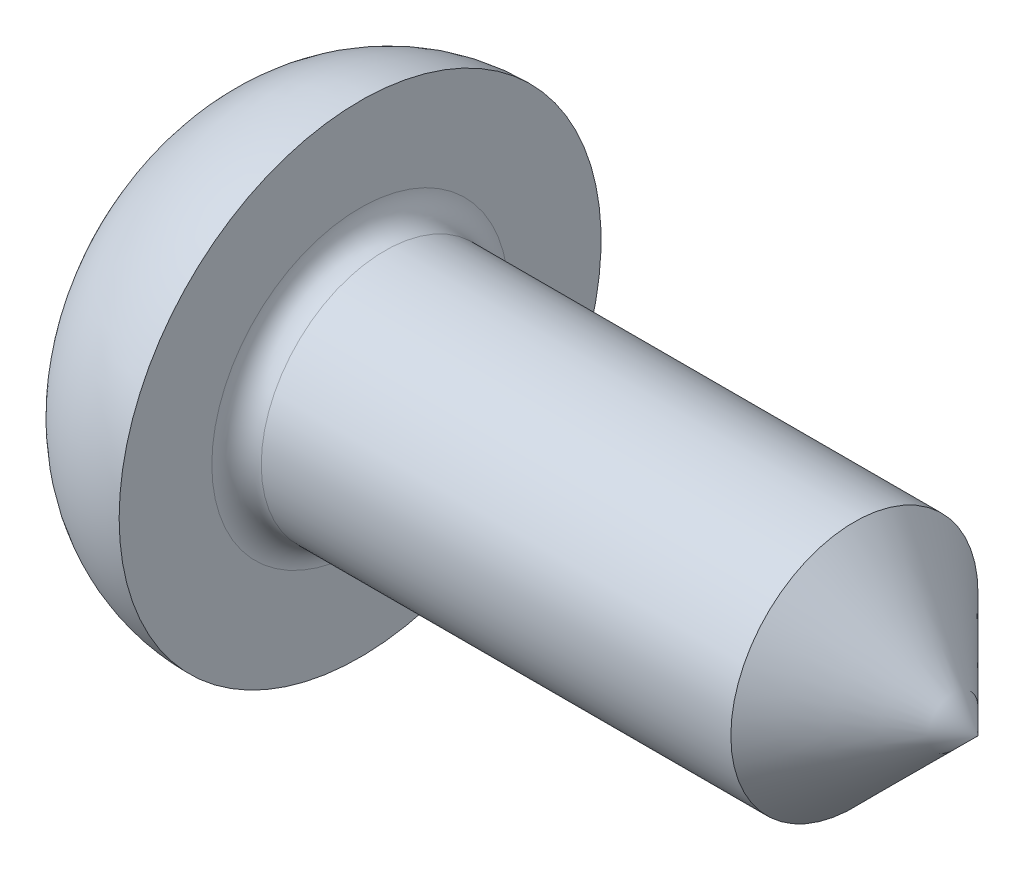
SolidWorks part; units mm, degrees
ref_plane "Front" through (0, 0, 0) normal (0, 0, 1) x (1, 0, 0)
ref_plane "Top" through (0, 0, 0) normal (0, 1, 0) x (1, 0, 0)
ref_plane "Right" through (0, 0, 0) normal (1, 0, 0) x (0, 0, -1)
sketch "Sketch1" plane through (0, 0, 0) normal (0, 1, 0) x (1, 0, 0)
  line L0 (-13.6293, 0) -> (11.3577, 0) construction
  line L1 (1.6, 1) -> (6.6, 1)
  line L2 (6.6, 1) -> (6.6, 0)
  line L3 (1.6, 1) -> (1.6, 1.95)
  line L4 (6.6, 0) -> (0, 0)
  arc A0 (1.6, 1.95) -> (0.4796, 1.4057) centre (1.5877, 0.5501) ccw
  arc A1 (0, 0) -> (0.4796, 1.4057) centre (2.3, 0) cw
  dimension "r2" = 1.4
  dimension "r1" = 2.3
  dimension "d" = 2
  dimension "dk" = 3.9
  dimension "k" = 1.6
  dimension "l" = 5
revolve "Revolve1" add sketch "Sketch1" angle 360 about L0
cosmetic thread "ThreadCosmetic1" [suppressed] parameters "l0"=4, "dm"=1.86
fillet "Fillet2" radius 0.2 1 edges at (1.6, 0, 1)
sketch "Sketch4" plane through (0, 0, 0) normal (0, 1, 0) x (1, 0, 0)
  line L0 (4.7828, 0) -> (7.1391, 0) construction
  line L2 (7.3335, 0) -> (7.3335, 21)
  line L3 (7.3335, 21) -> (-14.4, 21)
  line L4 (-14.4, 21) -> (6.6, 0)
  line L5 (6.6, 0) -> (7.3335, 0)
  line L7 (6.6, -1) -> (6.6, 1) construction
  dimension "D1" = 45
  dimension "D2" = 0.7335
  dimension "D3" = 21
revolve "Cut-Revolve1" cut sketch "Sketch4" angle 360 about L0
sketch "Sketch2" plane through (0, 0, 0) normal (1, 0, 0) x (0, 0, -1)
  line L0 (-2.278, 0) -> (2.6944, 0) construction
  line L1 (0, -2.1234) -> (0, 2.1948) construction
  line L2 (-0.3125, 0.3125) -> (-1.25, 0.3125)
  line L3 (0.3125, -1.25) -> (-0.3125, -1.25)
  line L4 (0.3125, -1.25) -> (0.3125, -0.3125)
  line L5 (0.3125, 1.25) -> (-0.3125, 1.25)
  line L6 (-0.3125, -1.25) -> (-0.3125, -0.3125)
  line L7 (1.25, 0.3125) -> (0.3125, 0.3125)
  line L8 (1.25, 0.3125) -> (1.25, -0.3125)
  line L9 (1.25, -0.3125) -> (0.3125, -0.3125)
  line L10 (-1.25, 0.3125) -> (-1.25, -0.3125)
  line L11 (-0.3125, 0.3125) -> (-0.3125, 1.25)
  line L12 (-0.3125, -0.3125) -> (-1.25, -0.3125)
  line L13 (0.3125, 0.3125) -> (0.3125, 1.25)
  point P19 (-0.3125, 0.3125)
  point P22 (0.3125, 0.3125)
  point P27 (-0.3125, -0.3125)
  dimension "m" = 2.5
  dimension "D2" = 2.5
  dimension "D3" = 0.625
  dimension "D4" = 0.625
ref_plane "Plane1" through (1.85, 0, 0) normal (1, 0, 0) x (0, 0, -1)
sketch "Sketch5" plane through (1.85, 0, 0) normal (1, 0, 0) x (0, 0, -1)
  point P0 (0, 0)
loft "Cut-Loft1" cut profiles "Sketch5", "Sketch2"
sketch "Sketch6" plane through (0, 0, 0) normal (0, 0, 1) x (1, 0, 0)
  line L0 (1.6, 1.2) -> (1.67, 1.2)
  line L1 (1.67, 1.2) -> (1.67, 1)
  line L2 (1.67, 1) -> (1.635, 0.9394)
  line L3 (1.6, 1) -> (1.635, 0.9394)
  line L4 (1.6, 1.2) -> (1.6, 1)
  line L5 (10.7743, 0) -> (0, 0) construction
  line L6 (1.6, 1) -> (1.67, 1) construction
  line L7 (1.635, 1) -> (1.635, 0.9394) construction
  line L8 (5.6, 1) -> (1.8, 1) construction
  point P5 (1.635, 1.2)
  dimension "D1" = 0.2
  dimension "D2" = 0.07
  dimension "D3" = 5
revolve "Cut-Revolve10" [suppressed] cut sketch "Sketch6" angle 360 about L5
pattern_linear "LPattern10" [suppressed] count 36 spacing 0.14 along (1, 0, 0)
equation "\"D4@Sketch2\" = \"D3@Sketch2\""
equation "\"D2@Sketch2\" = \"m@Sketch2\""
equation "\"D3@Sketch2\" = \"m@Sketch2\" / 4"
equation "\"D2@Sketch6\" = (  \"d@Sketch1\" - \"dm@ThreadCosmetic1\" )  / 2"
equation "\"D3@Sketch6\" = \"l0@ThreadCosmetic1\" + \"d@Sketch1\" / 2"
equation "\"D3@LPattern10\" = \"D2@Sketch6\" *2"
equation "\"D1@LPattern10\" = \"D3@Sketch6\" / \"D3@LPattern10\""
